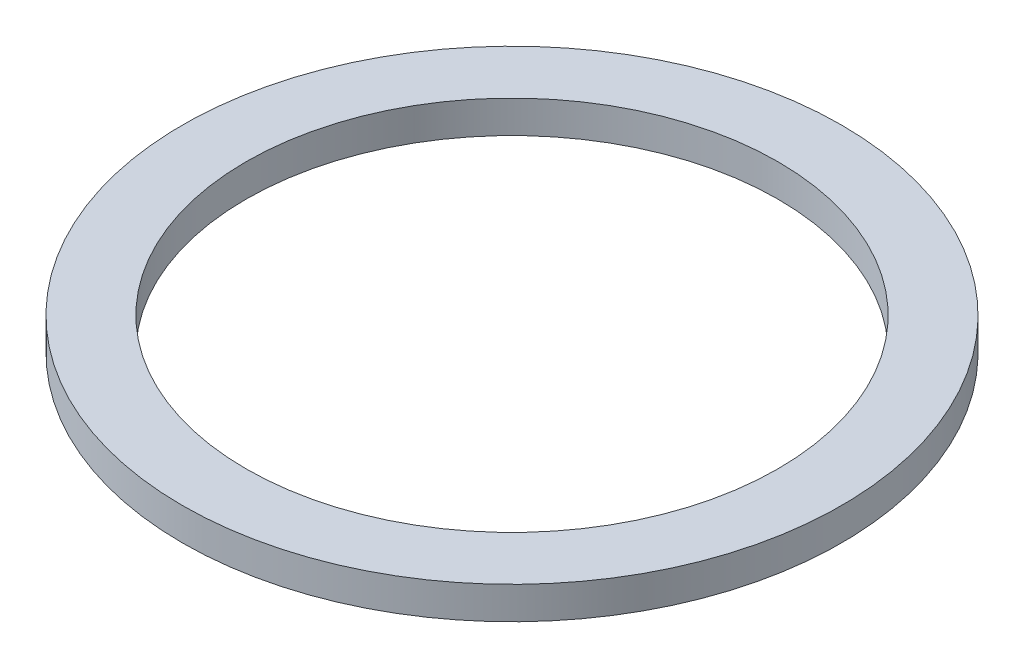
SolidWorks part; units mm, degrees
ref_plane "前视基准面" through (0, 0, 0) normal (0, 0, 1) x (1, 0, 0)
ref_plane "上视基准面" through (0, 0, 0) normal (0, 1, 0) x (1, 0, 0)
ref_plane "右视基准面" through (0, 0, 0) normal (1, 0, 0) x (0, 0, -1)
sketch "草图1" plane through (0, 0, 0) normal (0, 0, 1) x (1, 0, 0)
  line L0 (0, 77.1441) -> (0, -87.8701) construction
  line L1 (-61.6053, 0) -> (62.4304, 0) construction
  line L2 (20.5, 0) -> (20.5, 2.5)
  line L3 (25.4, 0) -> (25.4, 2.5)
  line L4 (20.5, 2.5) -> (25.4, 2.5)
  line L5 (20.5, 0) -> (25.4, 0)
  dimension "D1" = 20.5
  dimension "D2" = 25.4
  dimension "D3" = 2.5
revolve "旋转1" add sketch "草图1" angle 360 about L0
cosmetic thread "装饰螺纹线1" parameters "D2"=42
